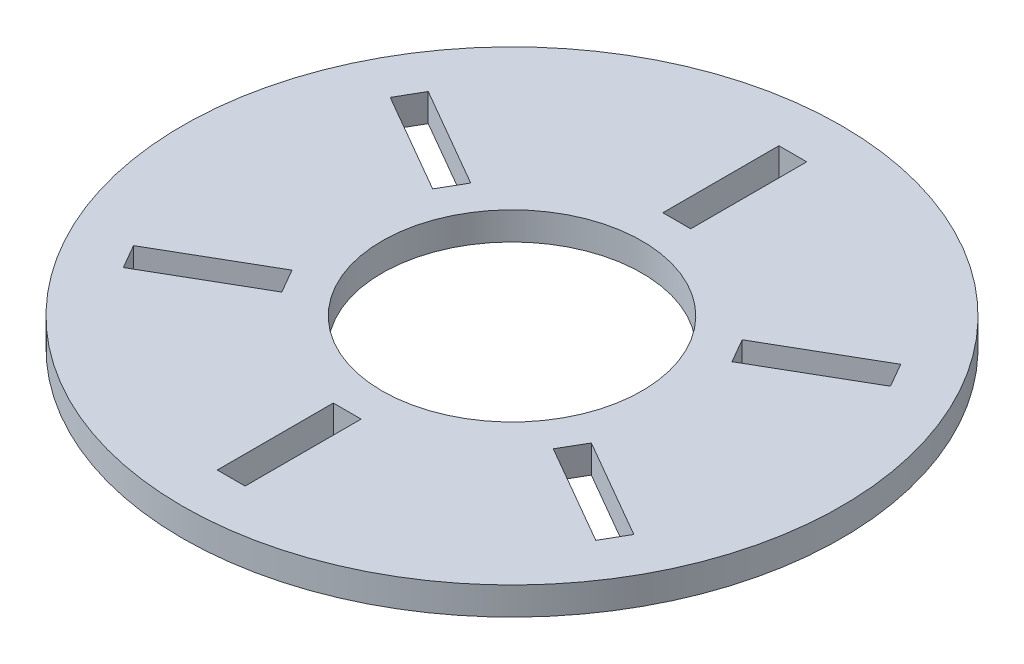
SolidWorks part; units mm, degrees
ref_plane "Plan de face" through (0, 0, 0) normal (0, 0, 1) x (1, 0, 0)
ref_plane "Plan de dessus" through (0, 0, 0) normal (0, 1, 0) x (1, 0, 0)
ref_plane "Plan de droite" through (0, 0, 0) normal (1, 0, 0) x (0, 0, -1)
sketch "Esquisse1" plane through (0, 0, 0) normal (0, 1, 0) x (1, 0, 0)
  circle A0 centre (0, 0) radius 28
  circle A1 centre (0, 0) radius 71
  dimension "D1" = 56
  dimension "D2" = 142
extrude "Boss.-Extru.1" add sketch "Esquisse1" along normal blind 6
sketch "Esquisse2" plane through (0, 0, 0) normal (0, -1, 0) x (1, 0, 0)
  line L0 (-71, 0) -> (71, 0) construction
  line L1 (0, 0) -> (0, 71) construction
  line L2 (0, 0) -> (0, -95.7485) construction
  line L3 (0, 0) -> (0, -48) construction
  line L4 (50.8945, -32.8481) -> (29.2439, -20.3481)
  line L5 (3, -60.5) -> (-3, -60.5)
  line L6 (3, -60.5) -> (3, -35.5)
  line L7 (3, -35.5) -> (-3, -35.5)
  line L8 (-3, -60.5) -> (-3, -35.5)
  line L9 (3, -60.5) -> (-3, -35.5) construction
  line L10 (3, -35.5) -> (-3, -60.5) construction
  line L11 (53.8945, -27.6519) -> (32.2439, -15.1519)
  line L12 (53.8945, -27.6519) -> (50.8945, -32.8481)
  line L13 (32.2439, -15.1519) -> (29.2439, -20.3481)
  line L14 (53.8945, 27.6519) -> (32.2439, 15.1519)
  line L15 (50.8945, 32.8481) -> (29.2439, 20.3481)
  line L16 (0, 0) -> (-89, 89) construction
  line L17 (50.8945, 32.8481) -> (53.8945, 27.6519)
  line L18 (29.2439, 20.3481) -> (32.2439, 15.1519)
  line L19 (3, 60.5) -> (3, 35.5)
  line L20 (-3, 60.5) -> (-3, 35.5)
  line L21 (-3, 60.5) -> (3, 60.5)
  line L22 (-3, 35.5) -> (3, 35.5)
  line L23 (-50.8945, 32.8481) -> (-29.2439, 20.3481)
  line L24 (-53.8945, 27.6519) -> (-32.2439, 15.1519)
  line L25 (-53.8945, 27.6519) -> (-50.8945, 32.8481)
  line L26 (-32.2439, 15.1519) -> (-29.2439, 20.3481)
  line L27 (-53.8945, -27.6519) -> (-32.2439, -15.1519)
  line L28 (-50.8945, -32.8481) -> (-29.2439, -20.3481)
  line L29 (-50.8945, -32.8481) -> (-53.8945, -27.6519)
  line L30 (-29.2439, -20.3481) -> (-32.2439, -15.1519)
  circle A0 centre (0, 0) radius 71 construction
  circle A1 centre (0, 0) radius 28 construction
  point P0 (0, 0)
  point P10 (0, -28)
  point P32 (0, -71)
  point P44 (0, 0)
  dimension "D1" = 48
  dimension "D2" = 43
  dimension "D3" = 28
  dimension "D4" = 25
  dimension "D5" = 6
  dimension "D6" = 6
extrude "Enlèv. mat.-Extru.1" cut sketch "Esquisse2" against normal blind 10
